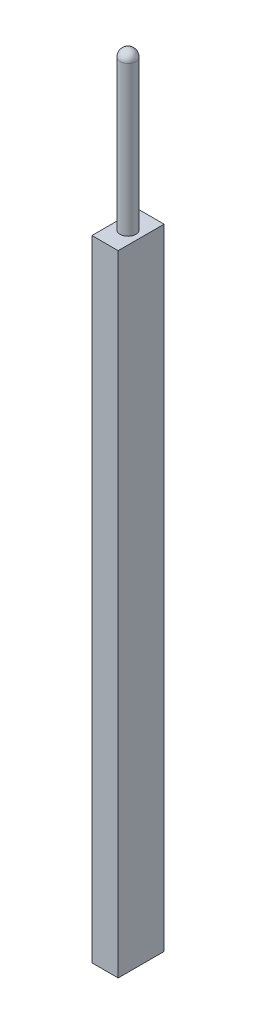
SolidWorks part; units mm, degrees
ref_plane "Piano frontale" through (0, 0, 0) normal (0, 0, 1) x (1, 0, 0)
ref_plane "Piano superiore" through (0, 0, 0) normal (0, 1, 0) x (1, 0, 0)
ref_plane "Piano destro" through (0, 0, 0) normal (1, 0, 0) x (0, 0, -1)
sketch "Schizzo1" plane through (0, 0, 0) normal (0, 0, 1) x (1, 0, 0)
  line L0 (0, 0) -> (0, 30) construction
  line L1 (-1.5, 0) -> (-1.5, 28.5)
  line L2 (-1.5, 0) -> (0, 0)
  line L3 (0, 0) -> (0, 30)
  arc A0 (0, 30) -> (-1.5, 28.5) centre (0, 28.5) ccw
  dimension "D3" = 1.5
  dimension "D1" = 30
  dimension "D2" = 3
revolve "Rivoluzione2" add sketch "Schizzo1" angle 360 about L0
sketch "Schizzo2" plane through (0, 0, 0) normal (0, -1, 0) x (1, 0, 0)
  line L1 (-2.5, -4.375) -> (2.5, -4.375)
  line L2 (-2.5, -4.375) -> (-2.5, 4.375)
  line L3 (-2.5, 4.375) -> (2.5, 4.375)
  line L4 (2.5, -4.375) -> (2.5, 4.375)
  line L5 (-2.5, -4.375) -> (2.5, 4.375) construction
  line L6 (-2.5, 4.375) -> (2.5, -4.375) construction
  point P0 (0, 0)
  dimension "D1" = 5
  dimension "D2" = 8.75
extrude "Estrusione-Estrusione1" add sketch "Schizzo2" along normal blind 120
